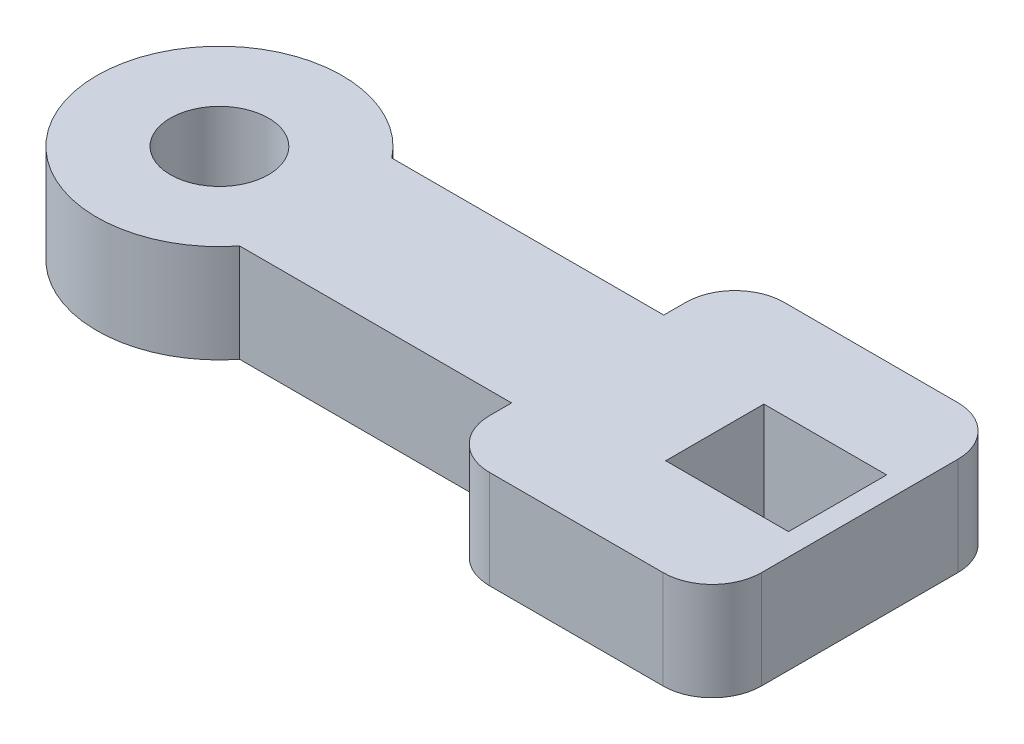
SolidWorks part; units mm, degrees
ref_plane "Front Plane" through (0, 0, 0) normal (0, 0, 1) x (1, 0, 0)
ref_plane "Top Plane" through (0, 0, 0) normal (0, 1, 0) x (1, 0, 0)
ref_plane "Right Plane" through (0, 0, 0) normal (1, 0, 0) x (0, 0, -1)
sketch "Sketch1" plane through (0, 0, 0) normal (0, 1, 0) x (1, 0, 0)
  line L0 (0, 0) -> (10, 0) construction
  line L1 (0, 0) -> (2.5, 0) construction
  line L2 (10, 1.55) -> (4.4615, 1.55)
  line L3 (10, -1.55) -> (4.4615, -1.55)
  line L4 (10, -1.55) -> (10, 1.55) construction
  line L5 (10, 0) -> (15.5385, 0) construction
  line L6 (10, -2) -> (10, 2)
  line L7 (15.5385, -2) -> (15.5385, 2)
  line L9 (11, -3) -> (14.5385, -3)
  line L10 (10, -3) -> (10, 3) construction
  line L11 (11, 3) -> (14.5385, 3)
  line L12 (15.5385, -3) -> (15.5385, 3) construction
  line L13 (12.5897, -1) -> (15.0897, -1)
  line L14 (12.5897, -1) -> (12.5897, 1)
  line L15 (12.5897, 1) -> (15.0897, 1)
  line L16 (15.0897, -1) -> (15.0897, 1)
  line L17 (12.5897, -1) -> (15.0897, 1) construction
  line L18 (12.5897, 1) -> (15.0897, -1) construction
  circle A0 centre (2.5, 0) radius 2.5 construction
  arc A1 (4.4615, 1.55) -> (4.4651, -1.5454) centre (2.5, 0) ccw
  arc A2 (15.5385, 2) -> (14.5385, 3) centre (14.5385, 2) ccw
  arc A3 (15.5385, -2) -> (14.5385, -3) centre (14.5385, -2) cw
  arc A4 (10, -2) -> (11, -3) centre (11, -2) ccw
  arc A5 (10, 2) -> (11, 3) centre (11, 2) cw
  circle A6 centre (2.5, 0) radius 1
  point P12 (10, 0)
  point P15 (10, 0)
  point P18 (15.5385, 0)
  point P30 (13.8397, 0)
  dimension "D3" = 6
  dimension "D5" = 1
  dimension "D9" = 2
  dimension "D1" = 10
  dimension "D2" = 2.5
  dimension "D4" = 3.1
  dimension "D6" = 2
  dimension "D7" = 2.5
  dimension "D8" = 0.4488
extrude "Boss-Extrude4" add sketch "Sketch1" along normal blind 2
